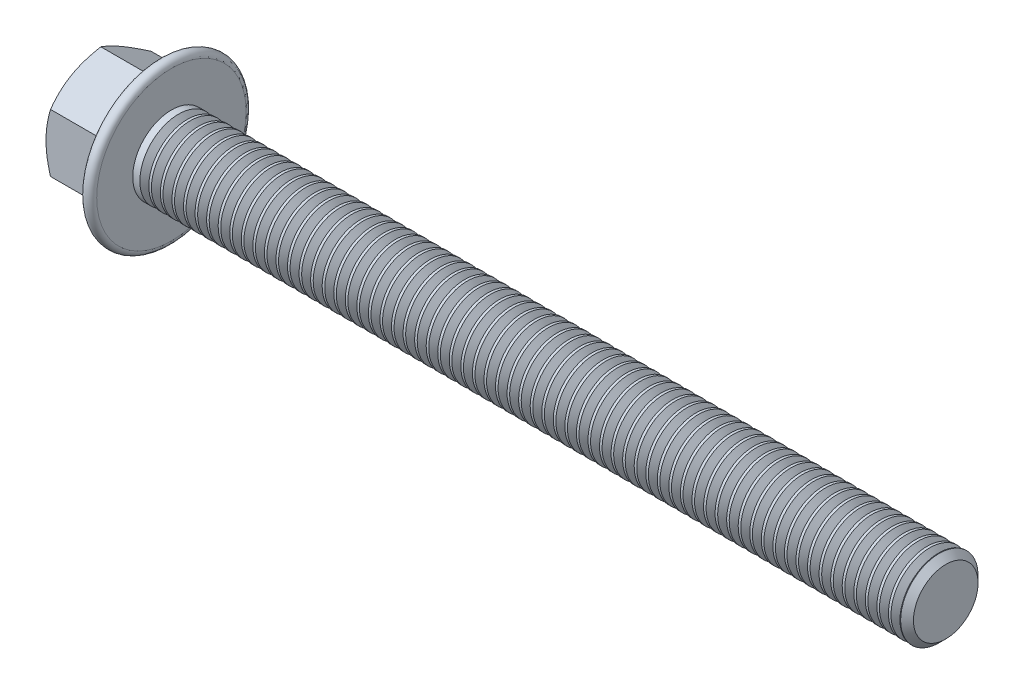
SolidWorks part; units mm, degrees
extrude "BaseHead" add sketch "Sketch1" along normal blind 9.7
sketch "Sketch1" plane through (0, 0, 0) normal (1, 0, 0) x (0, 0, -1)
  line L0 (6.5, 3.7528) -> (6.5, -3.7528)
  line L1 (-6.5, 3.7528) -> (-6.5, -3.7528)
  line L2 (6.5, -3.7528) -> (0, -7.5056)
  line L3 (0, -7.5056) -> (-6.5, -3.7528)
  line L4 (6.5, 3.7528) -> (0, 7.5056)
  line L5 (0, 7.5056) -> (-6.5, 3.7528)
  dimension "Width_flats" = 13
  dimension "D2" = 120
  dimension "D3" = 6.5
  dimension "D4" = 6.5
  dimension "D5" = 6.5
ref_plane "Plane1" through (0, 0, 0) normal (0, 0, 1) x (1, 0, 0)
ref_plane "Plane2" through (0, 0, 0) normal (0, 1, 0) x (1, 0, 0)
ref_plane "Plane3" through (0, 0, 0) normal (1, 0, 0) x (0, 0, -1)
sketch "BodySke" plane through (0, 0, 0) normal (0, 0, 1) x (1, 0, 0)
  line L0 (0, 3.7528) -> (0, -3.7528) construction
  line L1 (0, 0) -> (109.7, 0)
  line L2 (0, 0) -> (0, 5)
  line L3 (0, 5) -> (108.872, 5)
  line L4 (109.7, 0) -> (109.7, 4.172)
  line L5 (9.7, 7.5056) -> (9.7, 3.7528) construction
  line L6 (109.7, 4.172) -> (108.872, 5)
  line L7 (0, 0) -> (96.52, 0) construction
  line L8 (109.7, -4.172) -> (108.872, -5) construction
  line L9 (0, -5) -> (108.872, -5) construction
  line L10 (11.2, 15.24) -> (11.2, -1.27) construction
  line L11 (9.7, 15.24) -> (9.7, -1.27) construction
  line L12 (9.7, 3.7528) -> (9.7, -3.7528) construction
  dimension "Diameter" = 10
revolve "BaseBody" add sketch "BodySke"
cosmetic thread "ThreadCosmetic" [suppressed]
fillet "HeadFillet" [suppressed] radius 0.4
sketch "Sketch3" plane through (0, 0, 0) normal (0, 0, 1) x (1, 0, 0)
  line L0 (0, 6.5) -> (3.4673, 12.5056)
  line L1 (0, 7.5056) -> (0, 3.7528) construction
  line L2 (3.4673, 12.5056) -> (3.4673, 17.5056)
  line L3 (3.4673, 17.5056) -> (-10, 17.5056)
  line L4 (-10, 17.5056) -> (-10, 6.5)
  line L5 (-10, 6.5) -> (0, 6.5)
  line L6 (0, 0) -> (99.06, 0) construction
  line L7 (9.7, 7.5056) -> (0, 7.5056) construction
  dimension "D1" = 6.5
  dimension "D2" = 5
  dimension "D3" = 10
  dimension "D4" = 5
  dimension "Head_ch_ang" = 30
revolve "HeadChamfer" cut sketch "Sketch3" angle 360 about L6
sketch "Sketch4" plane through (0, 0, 0) normal (0, 0, 1) x (1, 0, 0)
  line L0 (4.6396, 0) -> (8.2452, 9.9065)
  line L1 (9.7, 7.5056) -> (9.7, 3.7528) construction
  line L2 (8.2, 34.3444) -> (8.2, 16.9779) construction
  line L3 (9.7, 0) -> (9.7, 9.65)
  line L4 (8.3021, 10.4) -> (20.1618, 10.4) construction
  line L5 (0, 0) -> (95.25, 0) construction
  line L6 (0, 0) -> (96.52, 0) construction
  line L7 (4.6396, 0) -> (9.7, 0)
  line L8 (8.3021, -10.4) -> (20.1618, -10.4) construction
  arc A0 (9.7, 9.65) -> (8.2452, 9.9065) centre (8.95, 9.65) ccw
  dimension "D1" = 20
  dimension "Flange_thickness" = 1.5
  dimension "Flange_dia" = 20.8
revolve "Flange" add sketch "Sketch4" angle 360 about L5
fillet "FlangeHexFillet" radius 0.2 6 edges
sketch "ThdSchSke" plane through (0, 0, 0) normal (0, 0, 1) x (1, 0, 0)
  line L0 (11.2, -4.172) -> (10.6202, -5)
  line L1 (11.2, -4.172) -> (11.7798, -5)
  line L2 (11.7798, -5) -> (11.7798, -6.25)
  line L3 (-3.175, 0) -> (5.1513, 0) construction
  line L5 (11.7798, -6.25) -> (10.6202, -6.25)
  line L6 (10.6202, -6.25) -> (10.6202, -5)
  dimension "Thread_minor" = 8.344
  dimension "Diameter" = 10
  dimension "Start" = 11.2
revolve "ThreadSchematic" cut sketch "ThdSchSke" angle 360 about L3
pattern_linear "ThdSchPat" count 66 spacing 1.4924 along (1, 0, 0) of "ThreadSchematic"
equation "\"D3@Sketch1\" = \"Width_flats@Sketch1\" / 2"
equation "\"D4@Sketch1\" = \"D3@Sketch1\""
equation "\"D5@Sketch1\" = \"D4@Sketch1\""
equation "\"Thread_minor@ThreadCosmetic\" = \"Minor_dia@BodySke\""
equation "\"D1@Sketch3\" = \"Width_flats@Sketch1\" / 2"
equation "\"Thread_length@ThreadCosmetic\" = ((sgn( (\"Length@BodySke\" - \"Advance@BodySke\" ) - \"Thread_nom@BodySke\" )-1)*( (\"Length@BodySke\" - \"Advance@BodySke\" ) - \"Thread_nom@BodySke\" ))/-2+ \"Thread_nom@BodySke\""
equation "\"Thread_minor@ThdSchSke\" = \"Minor_dia@BodySke\""
equation "\"Diameter@ThdSchSke\" = \"Diameter@BodySke\""
equation "\"Overcut@ThdSchSke\" = \"Diameter@BodySke\" * 1.25"
equation "\"Start@ThdSchSke\" = \"Head_ht@BaseHead\" + \"Length@BodySke\" - \"Thread_length@ThreadCosmetic\"  '---Non-countersunk---"
equation "\"Num_threads@ThdSchPat\" = int( \"Thread_length@ThreadCosmetic\" / \"Advance@BodySke\" + 0.999 )  + 1"
equation "\"Advance@ThdSchPat\" = \"Thread_length@ThreadCosmetic\" /  (\"Num_threads@ThdSchPat\" - 1) 'relax it"
equation "\"Num_threads@ThdSchPat\" = \"Num_threads@ThdSchPat\" - sgn( \"Num_threads@ThdSchPat\" - 1) '---chamfered tips only---"
